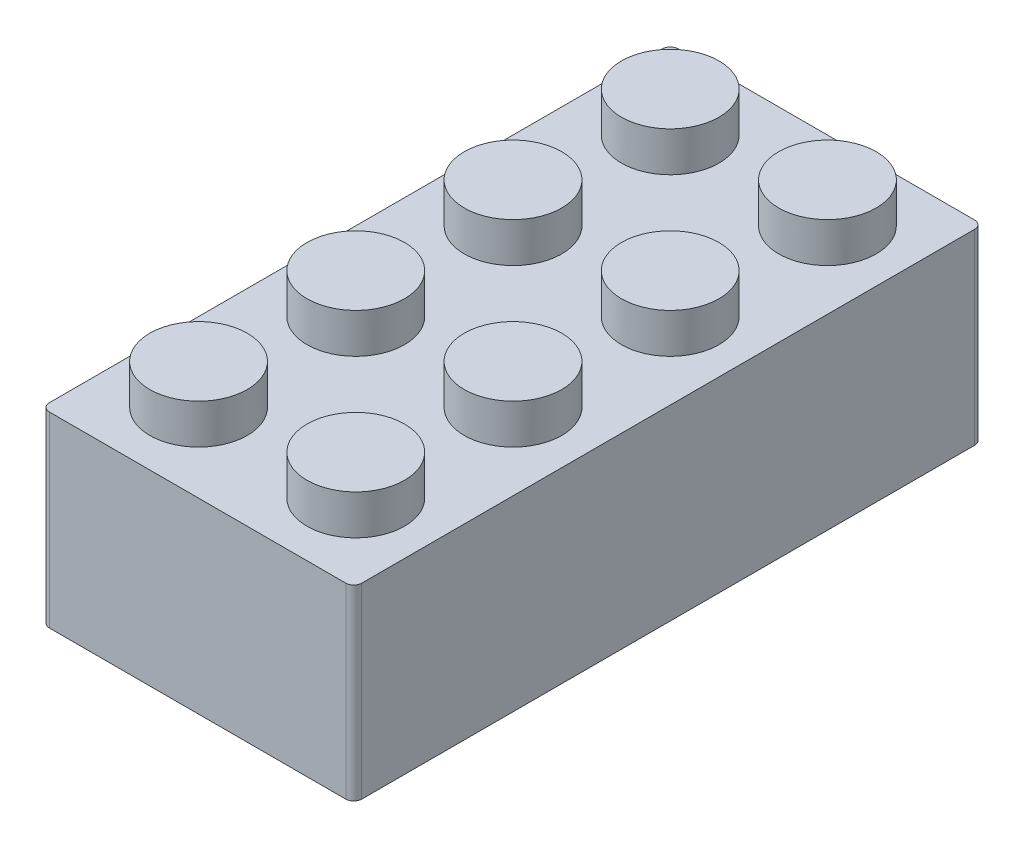
SolidWorks part; units mm, degrees
ref_plane "Front Plane" through (0, 0, 0) normal (0, 0, 1) x (1, 0, 0)
ref_plane "Top Plane" through (0, 0, 0) normal (0, 1, 0) x (1, 0, 0)
ref_plane "Right Plane" through (0, 0, 0) normal (1, 0, 0) x (0, 0, -1)
sketch "stencil" plane through (0, 0, 0) normal (0, 1, 0) x (1, 0, 0)
  line L2 (0, 0) -> (0, 31.5) construction
  line L29 (0, 0) -> (15.7, 0) construction
  line L30 (0, 3.95) -> (15.7, 3.95) construction
  line L31 (0, 7.9) -> (15.7, 7.9) construction
  line L32 (0, 11.85) -> (15.7, 11.85) construction
  line L33 (0, 15.8) -> (15.7, 15.8) construction
  line L34 (0, 19.75) -> (15.7, 19.75) construction
  line L35 (0, 23.7) -> (15.7, 23.7) construction
  line L36 (0, 27.65) -> (15.7, 27.65) construction
  line L37 (0, 31.6) -> (15.7, 31.6) construction
  line L38 (3.95, 0) -> (3.95, 31.5) construction
  line L39 (7.9, 0) -> (7.9, 31.5) construction
  line L40 (11.85, 0) -> (11.85, 31.5) construction
  line L41 (15.8, 0) -> (15.8, 31.5) construction
  line L42 (0, 31.6) -> (0, 0)
  line L43 (0, 0) -> (15.7, 0)
  line L44 (15.7, 0) -> (15.8, 31.5)
  line L45 (15.8, 31.5) -> (0, 31.5)
  circle A26 centre (3.95, 3.95) radius 2.45
  circle A27 centre (11.85, 3.95) radius 2.45
  circle A28 centre (11.85, 11.85) radius 2.45
  circle A29 centre (3.95, 11.85) radius 2.45
  circle A30 centre (11.85, 19.75) radius 2.45
  circle A31 centre (3.95, 19.75) radius 2.45
  circle A32 centre (11.85, 27.65) radius 2.45
  circle A33 centre (3.95, 27.65) radius 2.45
  circle A34 centre (7.85, 7.9) radius 3.2
  circle A35 centre (7.85, 7.9) radius 2.4
  circle A36 centre (7.85, 15.8) radius 2.4
  circle A37 centre (7.85, 15.8) radius 3.2
  circle A38 centre (7.85, 23.7) radius 2.4
  circle A39 centre (7.85, 23.7) radius 3.2
  point P6 (3.95, -15.8)
  point P9 (7.9, -15.8)
  point P10 (7.9, -11.85)
  point P13 (3.95, -7.9)
  point P15 (7.9, -7.9)
  point P17 (7.9, -3.95)
  point P18 (3.95, 0)
  point P21 (7.9, 0)
  point P25 (7.9, 3.95)
  point P27 (3.95, 7.9)
  point P28 (7.9, 7.9)
  point P29 (0, -11.85)
  point P30 (0, -7.9)
  point P31 (0, 3.95)
  point P34 (0, -3.95)
  point P36 (0, 15.8)
  point P37 (0, 23.7)
  point P38 (7.9, 23.7)
  point P39 (15.8, 23.7)
  point P40 (15.8, 15.8)
  point P41 (15.8, 7.9)
  dimension "D7" = 4.9
  dimension "D9" = 6.4
  dimension "D1" = 31.5
  dimension "D2" = 15.7
  dimension "D4" = 3.95
  dimension "D6" = 3.95
  dimension "D8" = 0.8
  dimension "D5" = 9
  dimension "D3" = 5
sketch "Sketch1" plane through (0, 0, 0) normal (0, 1, 0) x (1, 0, 0)
  line L17 (0, 0) -> (15.7, 0)
  line L18 (0, 0) -> (0, 31.6)
  line L19 (0, 31.6) -> (15.7, 31.6)
  line L20 (15.7, 0) -> (15.7, 31.6)
extrude "Boss-Extrude1" add sketch "Sketch1" along normal mid plane 9.4
sketch "Sketch2" plane through (0, 4.7, 0) normal (0, 1, 0) x (1, 0, 0)
  circle A3 centre (3.95, 3.95) radius 2.45
  circle A11 centre (11.85, 3.95) radius 2.45
  circle A12 centre (11.85, 11.85) radius 2.45
  circle A13 centre (3.95, 11.85) radius 2.45
  circle A14 centre (3.95, 19.75) radius 2.45
  circle A15 centre (11.85, 19.75) radius 2.45
  circle A16 centre (3.95, 27.65) radius 2.45
  circle A26 centre (3.95, 27.65) radius 2.45 construction
  circle A27 centre (11.85, 27.65) radius 2.45
extrude "Boss-Extrude2" add sketch "Sketch2" along normal blind 2
sketch "Sketch3" plane through (0, -4.7, 0) normal (0, -1, 0) x (1, 0, 0)
  line L0 (0, -15.8) -> (15.7, -15.8) construction
  line L5 (14.3, -30.2) -> (1.4, -30.2)
  line L7 (14.3, -30.2) -> (14.3, -1.4)
  line L15 (14.3, -1.4) -> (1.4, -1.4)
  line L16 (1.4, -30.2) -> (1.4, -1.4)
  line L17 (7.85, -1.4) -> (7.85, -30.2) construction
  line L18 (14.3, -15.8) -> (1.4, -15.8) construction
  line L19 (0, 0) -> (15.7, 0) construction
  line L20 (0, -31.6) -> (0, 0) construction
  point P0 (7.85, -15.8)
  dimension "D1" = 1.4
  dimension "D2" = 1.4
extrude "Cut-Extrude1" cut sketch "Sketch3" against normal blind 4
sketch "Sketch4" plane through (0, -0.7, 0) normal (0, -1, 0) x (1, 0, 0)
  line L0 (0, -7.9) -> (15.7, -7.9) construction
  line L1 (0, -15.8) -> (15.7, -15.8) construction
  line L2 (0, -23.7) -> (15.7, -23.7) construction
  circle A2 centre (7.85, -7.9) radius 3.2
  circle A3 centre (7.85, -7.9) radius 2.4
  circle A6 centre (7.85, -15.8) radius 3.2
  circle A7 centre (7.85, -15.8) radius 2.4
  circle A10 centre (7.85, -23.7) radius 3.2
  circle A11 centre (7.85, -23.7) radius 2.4
  circle A20 centre (7.85, -23.7) radius 2.4 construction
  circle A21 centre (7.85, -23.7) radius 3.2 construction
extrude "Boss-Extrude3" add sketch "Sketch4" along normal up to surface (4 mm away) up to face at (7.85, -4.7, -15.8)
fillet "Fillet1" radius 0.4 4 edges at (0, 0, -31.6) (15.7, 0, -31.6) (15.7, 0, 0) (0, 0, 0)
equation "\"t\"= 0.1'tolerance"
equation "\"D1@Sketch3\"= 1.5 - \"t\""
equation "\"D2@Sketch3\"=1.5-\"t\""
equation "\"D1@stencil\"=31.60mm-\"t\""
equation "\"D9@stencil\"=6.5-\"t\""
equation "\"D2@stencil\"=15.80-\"t\""
equation "\"D1@Boss-Extrude1\"=9.5-\"t\""
